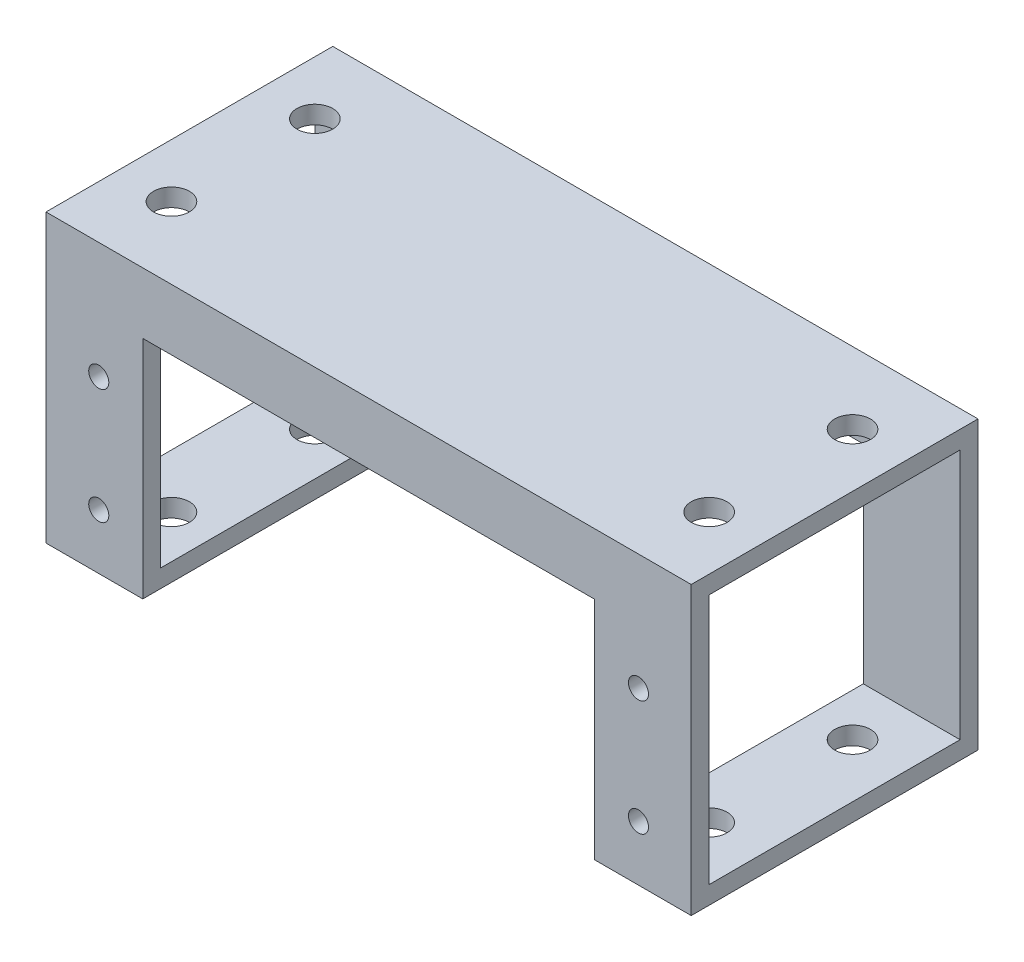
SolidWorks part; units mm, degrees
ref_plane "Front Plane" through (0, 0, 0) normal (0, 0, 1) x (1, 0, 0)
ref_plane "Top Plane" through (0, 0, 0) normal (0, 1, 0) x (1, 0, 0)
ref_plane "Right Plane" through (0, 0, 0) normal (1, 0, 0) x (0, 0, -1)
sketch "Sketch1" plane through (0, 0, 0) normal (1, 0, 0) x (0, 0, -1)
  line L0 (1.5875, 1.5875) -> (23.8125, 1.5875)
  line L1 (0, 0) -> (25.4, 0)
  line L2 (0, 0) -> (0, 25.4)
  line L3 (0, 25.4) -> (25.4, 25.4)
  line L4 (25.4, 0) -> (25.4, 25.4)
  line L5 (23.8125, 1.5875) -> (23.8125, 23.8125)
  line L6 (1.5875, 23.8125) -> (23.8125, 23.8125)
  line L7 (1.5875, 1.5875) -> (1.5875, 23.8125)
  dimension "D1" = 25.4
  dimension "D2" = 1.5875
extrude "Extrude1" add sketch "Sketch1" along normal blind 57.15
sketch "Sketch2" plane through (0, 0, 0) normal (0, 0, 1) x (1, 0, 0)
  line L0 (57.15, 0) -> (0, 0) construction
  line L1 (8.5725, 0) -> (48.5775, 0)
  line L2 (8.5725, 0) -> (8.5725, 19.9898)
  line L3 (8.5725, 19.9898) -> (48.5775, 19.9898)
  line L4 (48.5775, 0) -> (48.5775, 19.9898)
  line L5 (28.575, 31.2045) -> (28.575, -3.9333) construction
  line L6 (57.15, 25.4) -> (0, 25.4) construction
  point P10 (28.575, 25.4)
  point P11 (28.575, 19.9898)
  dimension "D1" = 40.005
  dimension "D2" = 19.9898
extrude "Cut-Extrude1" cut sketch "Sketch2" against normal up to next
sketch "Sketch3" plane through (0, 0, 0) normal (0, 0, 1) x (1, 0, 0)
  line L0 (2.291, 9.9949) -> (52.9691, 9.9949) construction
  line L1 (8.5725, 19.9898) -> (8.5725, 0) construction
  line L2 (28.575, 22.3865) -> (28.575, 0) construction
  line L3 (48.5775, 19.9898) -> (8.5725, 19.9898) construction
  circle A0 centre (4.6736, 15.1003) radius 0.889
  circle A1 centre (4.6736, 4.8895) radius 0.889
  circle A2 centre (52.4764, 15.1003) radius 0.889
  circle A3 centre (52.4764, 4.8895) radius 0.889
  point P4 (8.5725, 9.9949)
  point P17 (28.575, 19.9898)
  dimension "D1" = 1.778
  dimension "D2" = 10.2108
  dimension "D3" = 47.8028
extrude "Cut-Extrude2" cut sketch "Sketch3" against normal up to next
sketch "Sketch4" plane through (0, 25.4, 0) normal (0, 1, 0) x (1, 0, 0)
  line L0 (28.575, 31.0659) -> (28.575, -2.8244) construction
  line L1 (-6.2163, 12.7) -> (59.3466, 12.7) construction
  line L2 (0, 25.4) -> (0, 0) construction
  line L3 (57.15, 25.4) -> (0, 25.4) construction
  circle A0 centre (4.7625, 19.05) radius 1.5875
  circle A1 centre (4.7625, 6.35) radius 1.5875
  circle A2 centre (52.3875, 19.05) radius 1.5875
  circle A3 centre (52.3875, 6.35) radius 1.5875
  point P6 (0, 12.7)
  point P9 (28.575, 25.4)
  dimension "D3" = 3.175
  dimension "D1" = 47.625
  dimension "D2" = 12.7
extrude "Cut-Extrude3" cut sketch "Sketch4" against normal up to surface (25.4 mm away) up to face at (4.2863, 0, -12.7)
